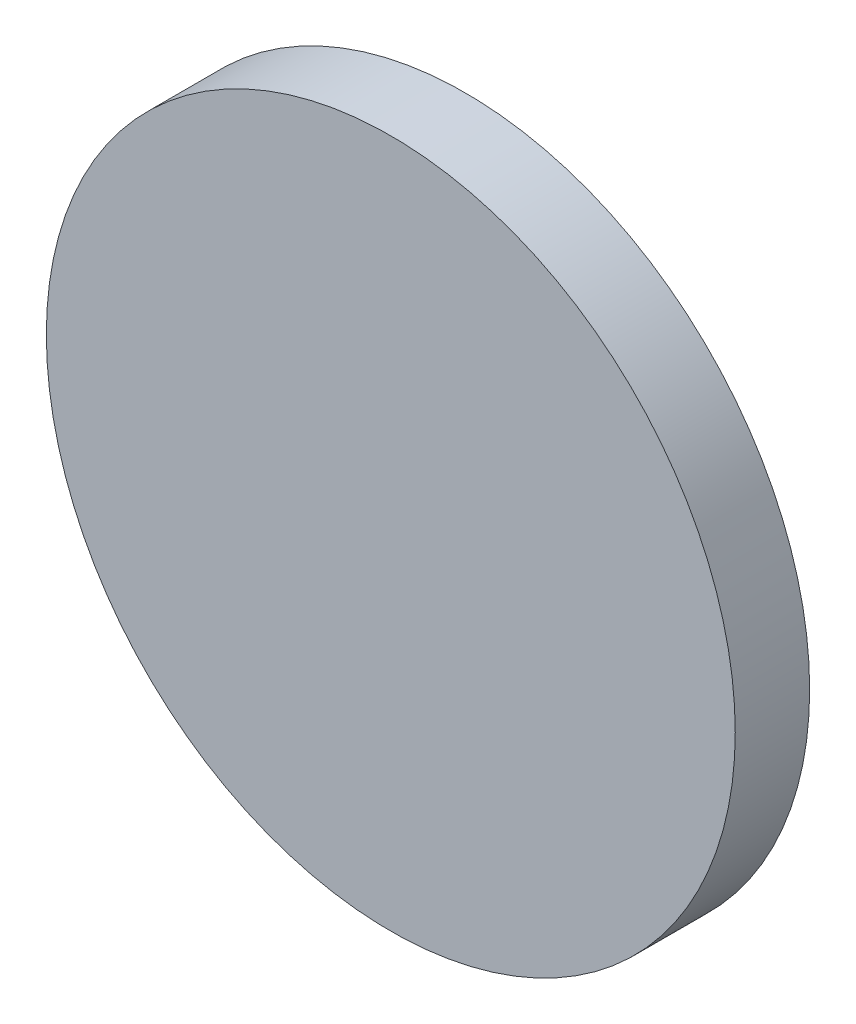
SolidWorks part; units mm, degrees
material "6061-T6 (SS)"
ref_plane "Front Plane" through (0, 0, 0) normal (0, 0, 1) x (1, 0, 0)
ref_plane "Top Plane" through (0, 0, 0) normal (0, 1, 0) x (1, 0, 0)
ref_plane "Right Plane" through (0, 0, 0) normal (1, 0, 0) x (0, 0, -1)
sketch "Sketch1" plane through (0, 0, 0) normal (0, 0, 1) x (1, 0, 0)
  circle A0 centre (0, 0) radius 32.0992
  dimension "D1" = 64.1985
extrude "Boss-Extrude1" add sketch "Sketch1" along normal blind 6.9342
